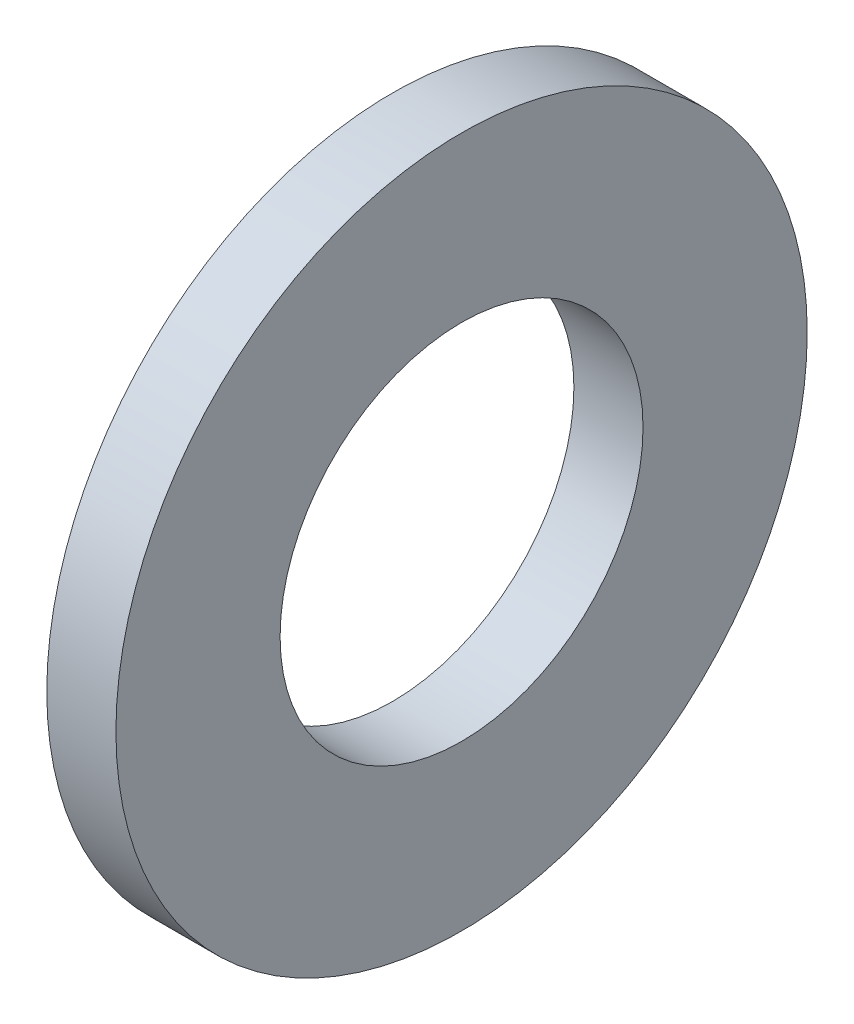
SolidWorks part; units mm, degrees
ref_plane "Plane1" through (0, 0, 0) normal (0, 0, 1) x (1, 0, 0)
ref_plane "Plane2" through (0, 0, 0) normal (0, 1, 0) x (1, 0, 0)
ref_plane "Plane3" through (0, 0, 0) normal (1, 0, 0) x (0, 0, -1)
sketch "Sketch1" plane through (0, 0, 0) normal (0, 0, 1) x (1, 0, 0)
  line L0 (-34.925, 0) -> (9.525, 0) construction
  line L1 (0, 5.25) -> (0, 10)
  line L2 (0, 10) -> (-2, 10)
  line L3 (-2, 10) -> (-2, 5.25)
  line L4 (-2, 5.25) -> (0, 5.25)
  dimension "Thickness" = 2
  dimension "Inside_dia" = 10.5
  dimension "Outside_dia" = 20
revolve "Base-Revolve" add sketch "Sketch1" angle 360 about L0
chamfer "ODChamfer" [suppressed] distance 0.5 angle 45
equation "\"D1@ODChamfer\" =  \"Thickness@Sketch1\" * 0.25"
